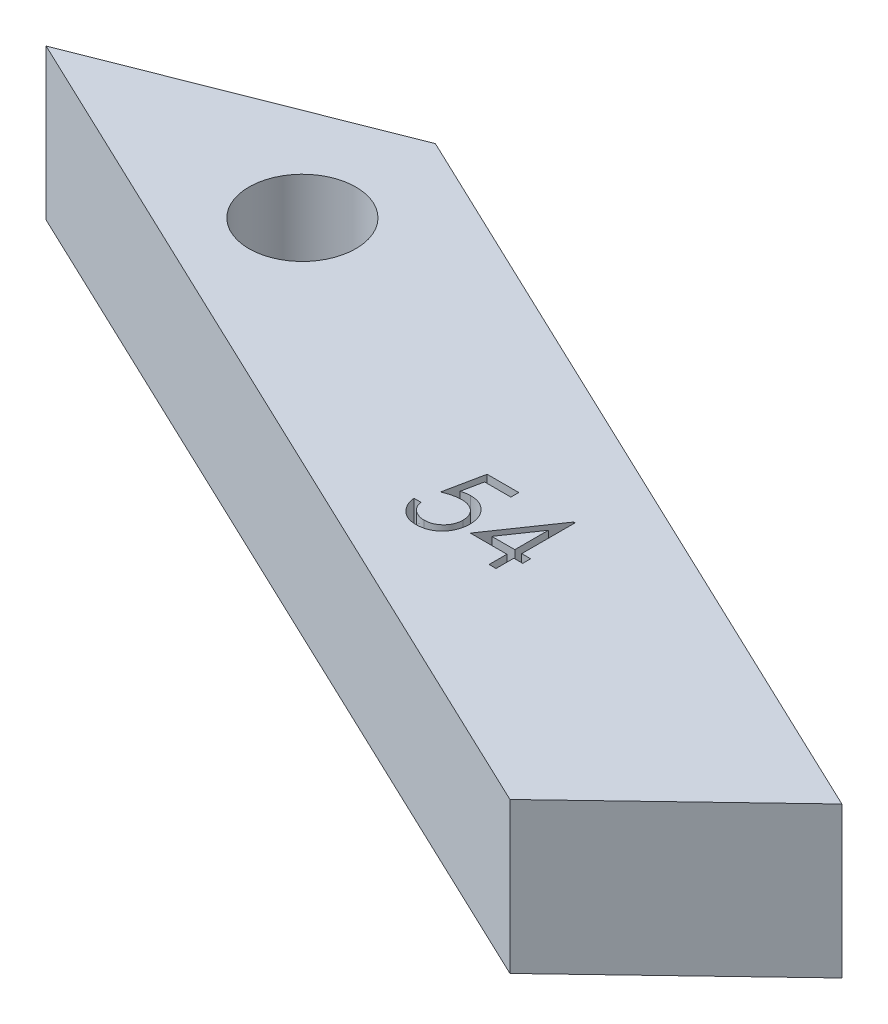
SolidWorks part; units mm, degrees
ref_plane "Front Plane" through (0, 0, 0) normal (0, 0, 1) x (1, 0, 0)
ref_plane "Top Plane" through (0, 0, 0) normal (0, 1, 0) x (1, 0, 0)
ref_plane "Right Plane" through (0, 0, 0) normal (1, 0, 0) x (0, 0, -1)
sketch "Sketch1" plane through (0, 0, 0) normal (0, 1, 0) x (-1, 0, 0)
  line L0 (-149.8064, 88.0436) -> (-144.2985, 82.2676)
  line L1 (-134.4358, 91.6725) -> (-127.4439, 98.3399)
  line L2 (-102.5471, 86.4995) -> (-91.0517, 81.0325)
  line L10 (-102.5385, 76.5028) -> (-81.1984, 84.9179)
  line L12 (-135.8612, 102.343) -> (-102.5471, 86.4995)
  line L13 (-102.5385, 76.5028) -> (-134.4358, 91.6725)
  line L14 (-135.8612, 102.343) -> (-149.8064, 88.0436)
  line L15 (-134.4358, 91.6725) -> (-149.8602, 76.9641)
  line L16 (-149.8602, 76.9641) -> (-173.8996, 100.0998)
  line L17 (-167.8618, 106.1279) -> (-149.8064, 88.0436)
  line L18 (-167.8618, 106.1279) -> (-173.8996, 100.0998)
  circle A1 centre (-134.7796, 96.3447) radius 2.2
  circle A2 centre (-168.0878, 100.0957) radius 2.2
  circle A3 centre (-149.935, 82.7336) radius 2.2
  circle A4 centre (-102.4484, 81.8835) radius 2.2
  point P3 (-149.935, 82.7336)
  point P25 (-102.5385, 76.5028)
  point P26 (-102.5471, 86.4995)
  point P29 (-135.8612, 102.343)
  point P30 (-149.8064, 88.0436)
  point P35 (-149.8602, 76.9641)
  point P37 (-167.8618, 106.1279)
  point P38 (-173.8996, 100.0998)
extrude "Boss-Extrude1" add sketch "Sketch1" along normal blind 6.2 contours L13 L10 L2 L12 L1 A4
sketch "Sketch2" plane through (0, 6.2, 0) normal (0, 1, 0) x (1, 0, 0)
  text T0 "54"
extrude "Cut-Extrude1" cut sketch "Sketch2" against normal blind 1
